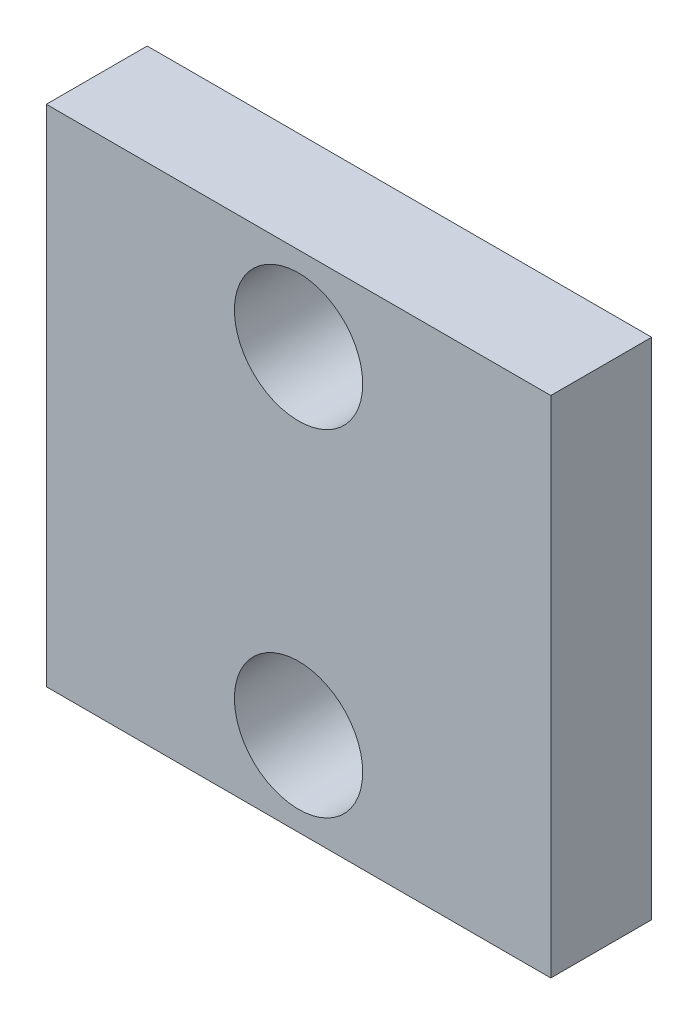
SolidWorks part; units mm, degrees
ref_plane "Plan de face" through (0, 0, 0) normal (0, 0, 1) x (1, 0, 0)
ref_plane "Plan de dessus" through (0, 0, 0) normal (0, 1, 0) x (1, 0, 0)
ref_plane "Plan de droite" through (0, 0, 0) normal (1, 0, 0) x (0, 0, -1)
sketch "Esquisse2" plane through (0, 0, 0) normal (0, 0, 1) x (1, 0, 0)
  line L1 (-30, -30) -> (30, -30)
  line L2 (-30, -30) -> (-30, 30)
  line L3 (-30, 30) -> (30, 30)
  line L4 (30, -30) -> (30, 30)
  line L5 (-30, -30) -> (30, 30) construction
  line L6 (-30, 30) -> (30, -30) construction
  circle A0 centre (0, 20) radius 7.6273
  circle A1 centre (0, -20) radius 7.6273
  point P0 (0, 0)
  point P10 (0, 21.7544)
  point P11 (0, -20)
  point P12 (0, -20)
  dimension "D1" = 20
  dimension "D2" = 60
  dimension "D3" = 40
extrude "Boss.-Extru.3" add sketch "Esquisse2" along normal blind 12
